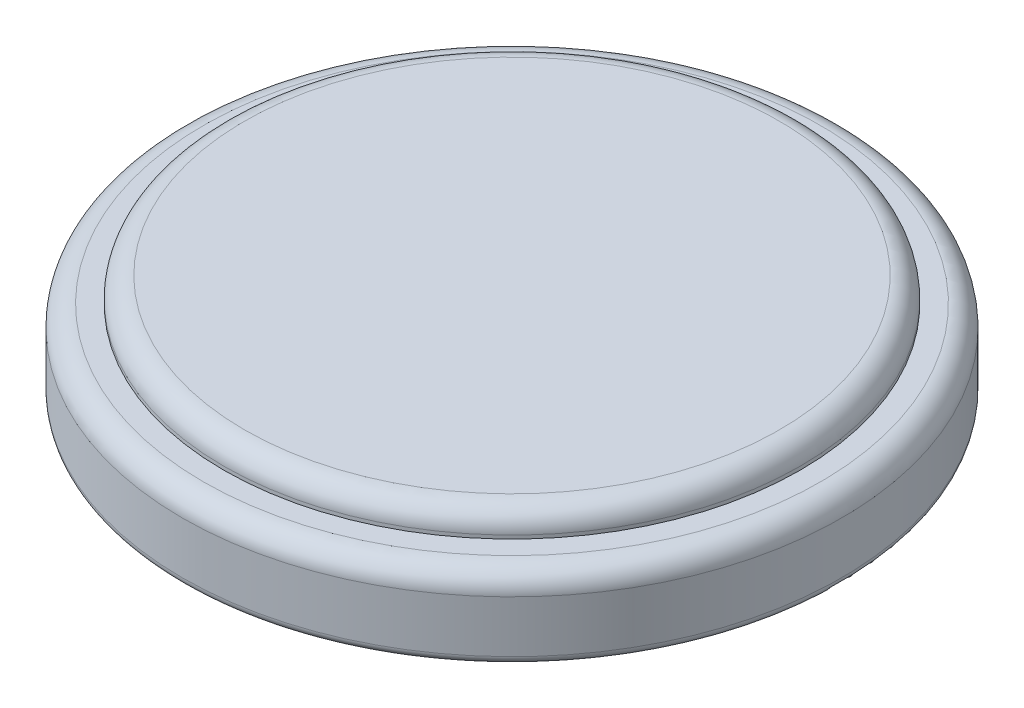
SolidWorks part; units mm, degrees
ref_plane "Front Plane" through (0, 0, 0) normal (0, 0, 1) x (1, 0, 0)
ref_plane "Top Plane" through (0, 0, 0) normal (0, 1, 0) x (1, 0, 0)
ref_plane "Right Plane" through (0, 0, 0) normal (1, 0, 0) x (0, 0, -1)
sketch "Sketch1" plane through (0, 0, 0) normal (0, 0, 1) x (1, 0, 0)
  line L0 (0, 0) -> (0, 3.2)
  line L1 (8.75, 2.46) -> (10, 2.46)
  line L2 (10, 2.46) -> (10, 0)
  line L3 (10, 0) -> (0, 0)
  line L4 (8.75, 2.46) -> (8.75, 3.2)
  line L5 (8.75, 3.2) -> (0, 3.2)
  dimension "D1" = 3.2
  dimension "D2" = 8.75
  dimension "D3" = 10
  dimension "D4" = 2.46
revolve "Revolve1" add sketch "Sketch1" angle 360 about L0
fillet "Fillet1" radius 0.635 2 edges at (0, 3.2, -8.75) (0, 2.46, -10)
fillet "Fillet2" radius 0.254 1 edges at (0, 0, -10)
